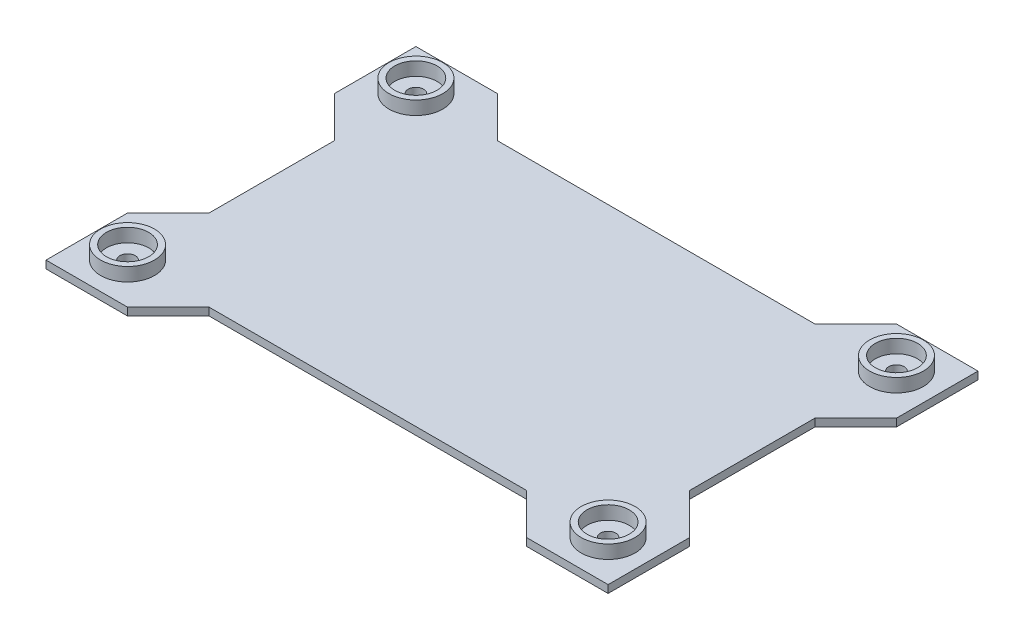
SolidWorks part; units mm, degrees
ref_plane "Front Plane" through (0, 0, 0) normal (0, 0, 1) x (1, 0, 0)
ref_plane "Top Plane" through (0, 0, 0) normal (0, 1, 0) x (1, 0, 0)
ref_plane "Right Plane" through (0, 0, 0) normal (1, 0, 0) x (0, 0, -1)
sketch "Sketch2" plane through (0, 0, 0) normal (0, 1, 0) x (1, 0, 0)
  line L1 (-125, 75) -> (125, 75)
  line L2 (-125, 75) -> (-125, -75)
  line L3 (-125, -75) -> (125, -75)
  line L4 (125, 75) -> (125, -75)
  line L5 (-125, 75) -> (125, -75) construction
  line L6 (-125, -75) -> (125, 75) construction
  point P0 (0, 0)
  dimension "D1" = 250
  dimension "D2" = 150
extrude "Boss-Extrude1" add sketch "Sketch2" along normal blind 4
sketch "Sketch3" plane through (0, 4, 0) normal (0, 1, 0) x (1, 0, 0)
  line L0 (-103.7868, 96.2132) -> (-82.5736, 75)
  line L1 (-146.2132, 96.2132) -> (-103.7868, 96.2132)
  line L2 (-146.2132, 96.2132) -> (-146.2132, 53.7868)
  line L5 (-146.2132, 96.2132) -> (-125, 75) construction
  line L6 (-146.2132, 53.7868) -> (-103.7868, 96.2132) construction
  line L7 (125, 75) -> (-125, 75) construction
  line L8 (-82.5736, 75) -> (-125, 75)
  line L9 (-146.2132, 53.7868) -> (-125, 32.5736)
  line L10 (-125, 75) -> (-125, -75) construction
  line L11 (-125, 32.5736) -> (-125, 75)
  point P0 (-125, 75)
  dimension "D1" = 45
  dimension "D2" = 45
  dimension "D3" = 30
extrude "Boss-Extrude2" add sketch "Sketch3" against normal up to surface (4 mm away) up to face at (0, 0, 0)
sketch "Sketch4" plane through (0, 4, 0) normal (0, 1, 0) x (1, 0, 0)
  line L0 (-146.2132, 53.7868) -> (-103.7868, 96.2132) construction
  circle A0 centre (-125, 75) radius 4
  point P6 (-125, 75)
  dimension "D1" = 8
extrude "Cut-Extrude1" cut sketch "Sketch4" against normal through all
sketch "Sketch5" plane through (0, 4, 0) normal (0, 1, 0) x (1, 0, 0)
  circle A0 centre (-125, 75) radius 11
  circle A3 centre (-125, 75) radius 14
  dimension "D1" = 22
  dimension "D2" = 3
extrude "Boss-Extrude3" add sketch "Sketch5" along normal blind 7
mirror "Mirror1" about plane through (0, 0, 0) normal (1, 0, 0) of "Boss-Extrude2", "Boss-Extrude3", "Cut-Extrude1"
mirror "Mirror2" about plane through (0, 0, 0) normal (0, 0, 1) of "Boss-Extrude2", "Cut-Extrude1", "Boss-Extrude3", "Mirror1"
